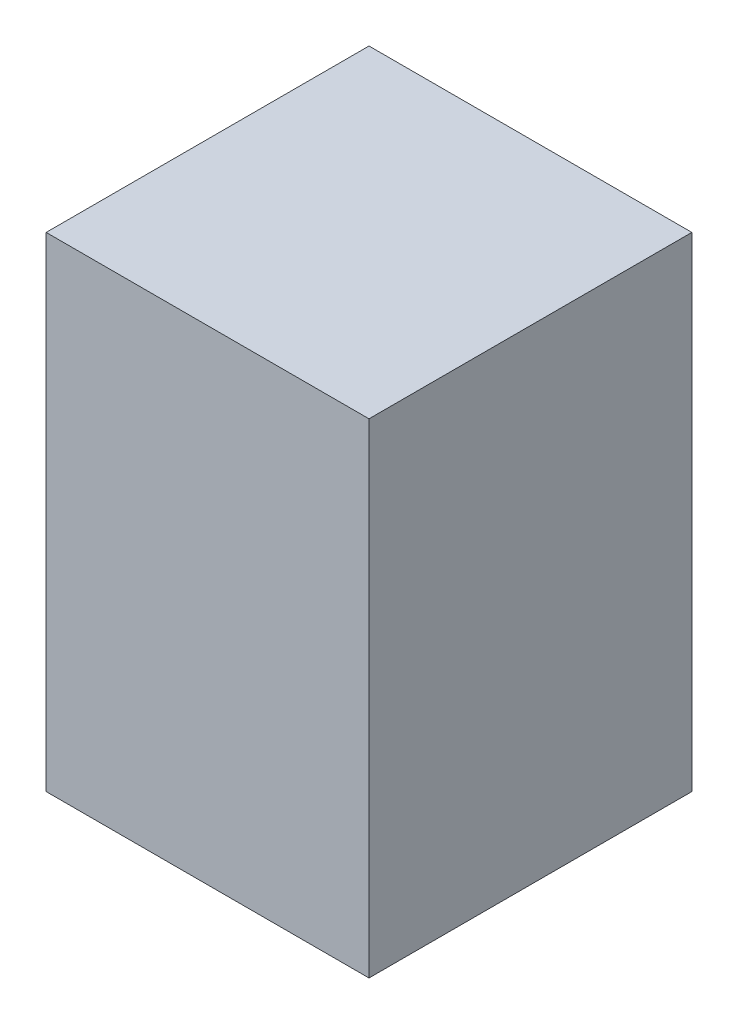
SolidWorks part; units mm, degrees
ref_plane "Front Plane" through (0, 0, 0) normal (0, 0, 1) x (1, 0, 0)
ref_plane "Top Plane" through (0, 0, 0) normal (0, 1, 0) x (1, 0, 0)
ref_plane "Right Plane" through (0, 0, 0) normal (1, 0, 0) x (0, 0, -1)
sketch "Sketch2" plane through (0, 0, 0) normal (0, 1, 0) x (1, 0, 0)
  line L1 (-182.562, 72.4647) -> (20.638, 72.4647)
  line L2 (-182.562, 72.4647) -> (-182.562, -130.7353)
  line L3 (-182.562, -130.7353) -> (20.638, -130.7353)
  line L4 (20.638, 72.4647) -> (20.638, -130.7353)
  dimension "D1" = 203.2
  dimension "D2" = 203.2
extrude "Boss-Extrude1" add sketch "Sketch2" along normal blind 304.8
